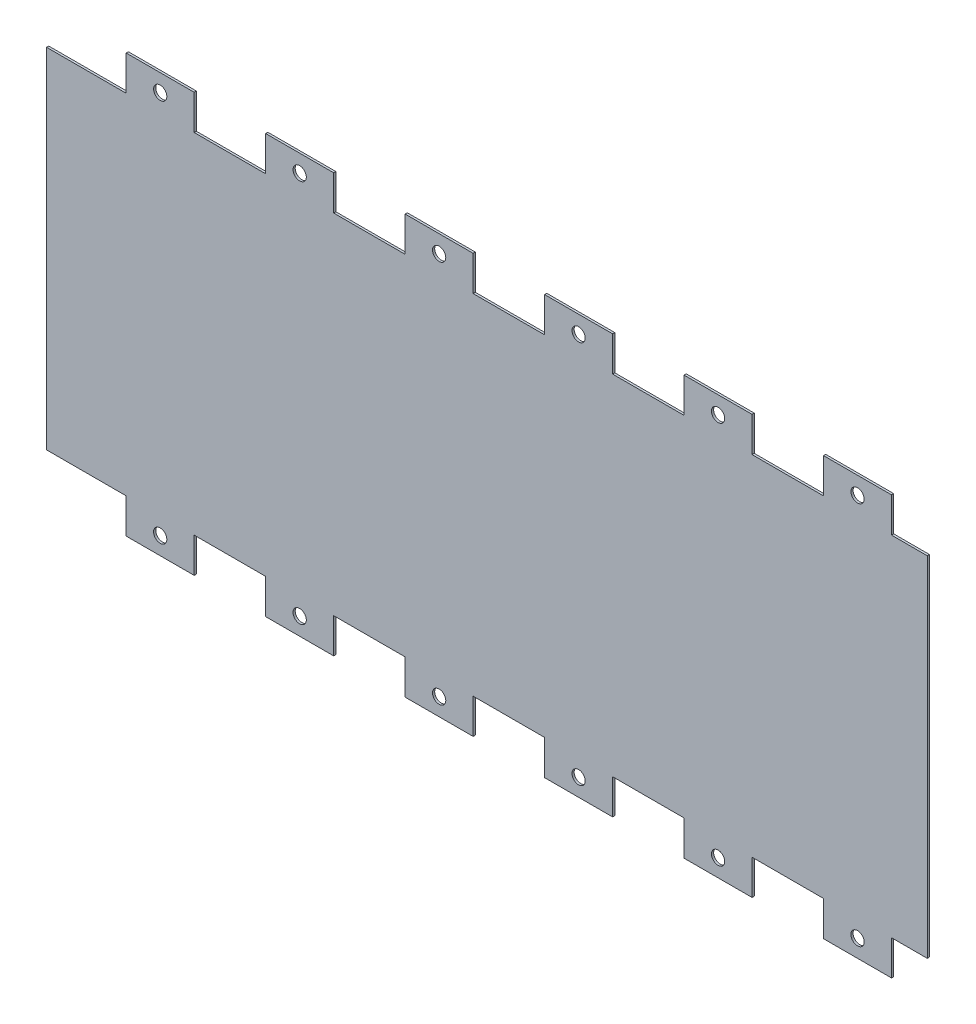
SolidWorks part; units mm, degrees
material "6061-T6 (SS)"
ref_plane "Front Plane" through (0, 0, 0) normal (0, 0, 1) x (1, 0, 0)
ref_plane "Top Plane" through (0, 0, 0) normal (0, 1, 0) x (1, 0, 0)
ref_plane "Right Plane" through (0, 0, 0) normal (1, 0, 0) x (0, 0, -1)
sketch "Sketch1" plane through (0, 0, 0) normal (0, 0, 1) x (1, 0, 0)
  line L1 (0, 0) -> (320.802, 0)
  line L2 (0, 0) -> (0, 152.4)
  line L3 (0, 152.4) -> (320.802, 152.4)
  line L4 (320.802, 0) -> (320.802, 152.4)
  dimension "D1" = 152.4
  dimension "D2" = 320.802
extrude "Boss-Extrude1" add sketch "Sketch1" along normal blind 0.7937
sketch "Sketch2" plane through (0, 0, 0.7937) normal (0, 0, 1) x (1, 0, 0)
  line L0 (320.802, 152.4) -> (0, 152.4) construction
  line L1 (320.802, 152.4) -> (307.7845, 152.4)
  line L2 (320.802, 152.4) -> (320.802, 139.7)
  line L3 (320.802, 139.7) -> (307.7845, 139.7)
  line L4 (307.7845, 152.4) -> (307.7845, 139.7)
  line L5 (283.0195, 152.4) -> (256.9845, 152.4)
  line L6 (283.0195, 152.4) -> (283.0195, 139.7)
  line L7 (283.0195, 139.7) -> (256.9845, 139.7)
  line L8 (256.9845, 152.4) -> (256.9845, 139.7)
  line L9 (206.1845, 152.4) -> (206.1845, 139.7)
  line L10 (232.2195, 152.4) -> (206.1845, 152.4)
  line L11 (232.2195, 152.4) -> (232.2195, 139.7)
  line L12 (232.2195, 139.7) -> (206.1845, 139.7)
  line L13 (155.3845, 152.4) -> (155.3845, 139.7)
  line L14 (181.4195, 152.4) -> (155.3845, 152.4)
  line L15 (181.4195, 152.4) -> (181.4195, 139.7)
  line L16 (181.4195, 139.7) -> (155.3845, 139.7)
  line L17 (104.5845, 152.4) -> (104.5845, 139.7)
  line L18 (130.6195, 152.4) -> (104.5845, 152.4)
  line L19 (130.6195, 152.4) -> (130.6195, 139.7)
  line L20 (130.6195, 139.7) -> (104.5845, 139.7)
  line L21 (53.7845, 152.4) -> (53.7845, 139.7)
  line L22 (79.8195, 152.4) -> (53.7845, 152.4)
  line L23 (79.8195, 152.4) -> (79.8195, 139.7)
  line L24 (79.8195, 139.7) -> (53.7845, 139.7)
  line L25 (2.9845, 152.4) -> (2.9845, 139.7)
  line L26 (29.0195, 152.4) -> (2.9845, 152.4)
  line L27 (29.0195, 152.4) -> (29.0195, 139.7)
  line L28 (29.0195, 139.7) -> (2.9845, 139.7)
  line L29 (0, 76.2) -> (320.802, 76.2) construction
  line L30 (0, 152.4) -> (2.9845, 152.4)
  line L31 (0, 152.4) -> (0, 139.7)
  line L32 (0, 139.7) -> (2.9845, 139.7)
  line L33 (2.9845, 152.4) -> (2.9845, 139.7)
  line L34 (0, 152.4) -> (0, 0) construction
  line L35 (320.802, 0) -> (320.802, 152.4) construction
  line L36 (2.9845, 0) -> (2.9845, 12.7)
  line L37 (0, 12.7) -> (2.9845, 12.7)
  line L38 (0, 0) -> (0, 12.7)
  line L39 (0, 0) -> (2.9845, 0)
  line L40 (29.0195, 12.7) -> (2.9845, 12.7)
  line L41 (29.0195, 0) -> (29.0195, 12.7)
  line L42 (29.0195, 0) -> (2.9845, 0)
  line L43 (2.9845, 0) -> (2.9845, 12.7)
  line L44 (79.8195, 12.7) -> (53.7845, 12.7)
  line L45 (79.8195, 0) -> (79.8195, 12.7)
  line L46 (79.8195, 0) -> (53.7845, 0)
  line L47 (53.7845, 0) -> (53.7845, 12.7)
  line L48 (130.6195, 12.7) -> (104.5845, 12.7)
  line L49 (130.6195, 0) -> (130.6195, 12.7)
  line L50 (130.6195, 0) -> (104.5845, 0)
  line L51 (104.5845, 0) -> (104.5845, 12.7)
  line L52 (181.4195, 12.7) -> (155.3845, 12.7)
  line L53 (181.4195, 0) -> (181.4195, 12.7)
  line L54 (181.4195, 0) -> (155.3845, 0)
  line L55 (155.3845, 0) -> (155.3845, 12.7)
  line L56 (232.2195, 12.7) -> (206.1845, 12.7)
  line L57 (232.2195, 0) -> (232.2195, 12.7)
  line L58 (232.2195, 0) -> (206.1845, 0)
  line L59 (206.1845, 0) -> (206.1845, 12.7)
  line L60 (256.9845, 0) -> (256.9845, 12.7)
  line L61 (283.0195, 12.7) -> (256.9845, 12.7)
  line L62 (283.0195, 0) -> (283.0195, 12.7)
  line L63 (283.0195, 0) -> (256.9845, 0)
  line L64 (307.7845, 0) -> (307.7845, 12.7)
  line L65 (320.802, 12.7) -> (307.7845, 12.7)
  line L66 (320.802, 0) -> (320.802, 12.7)
  line L67 (320.802, 0) -> (307.7845, 0)
  line M25 (0, 152.4) -> (0, 0)
  line M26 (0, 0) -> (320.802, 0)
  line M27 (320.802, 0) -> (320.802, 152.4)
  line M28 (320.802, 152.4) -> (0, 152.4)
  dimension "D1" = 13.0175
  dimension "D2" = 12.7
  dimension "D3" = 12.7
  dimension "D4" = 24.765
  dimension "D5" = 26.035
  dimension "D6" = 6
extrude "Cut-Extrude1" cut sketch "Sketch2" against normal through all contours L4 L3 M28 M27 | L8 L7 L6 M28 | L12 L11 L9 M28 | L16 L15 L13 M28 | L20 L19 L17 M28 | L24 L23 L21 M28 | L28 L27 L25 M28 | L32 L25 M25 M28 | L37 L36 M25 M26 | L41 L40 L36 M26 | L47 L45 L44 M26 | L51 L49 L48 M26 | L55 L53 L52 M26 | L59 L57 L56 M26 | L62 L61 L60 M26 | L65 L64 M27 M26
sketch "Sketch3" plane through (0, 0, 0.7937) normal (0, 0, 1) x (1, 0, 0)
  line L0 (29.0195, 152.4) -> (53.7845, 139.7) construction
  circle A0 centre (41.402, 146.05) radius 2.413
  circle A1 centre (92.202, 146.05) radius 2.413
  circle A2 centre (143.002, 146.05) radius 2.413
  circle A3 centre (193.802, 146.05) radius 2.413
  circle A4 centre (244.602, 146.05) radius 2.413
  circle A5 centre (295.402, 146.05) radius 2.413
  circle A6 centre (92.202, 6.35) radius 2.413
  circle A7 centre (143.002, 6.35) radius 2.413
  circle A8 centre (193.802, 6.35) radius 2.413
  circle A9 centre (244.602, 6.35) radius 2.413
  circle A10 centre (295.402, 6.35) radius 2.413
  circle A11 centre (41.402, 6.35) radius 2.413
  dimension "D1" = 4.826
  dimension "D2" = 6
  dimension "D3" = 2
extrude "Cut-Extrude2" cut sketch "Sketch3" against normal through all
